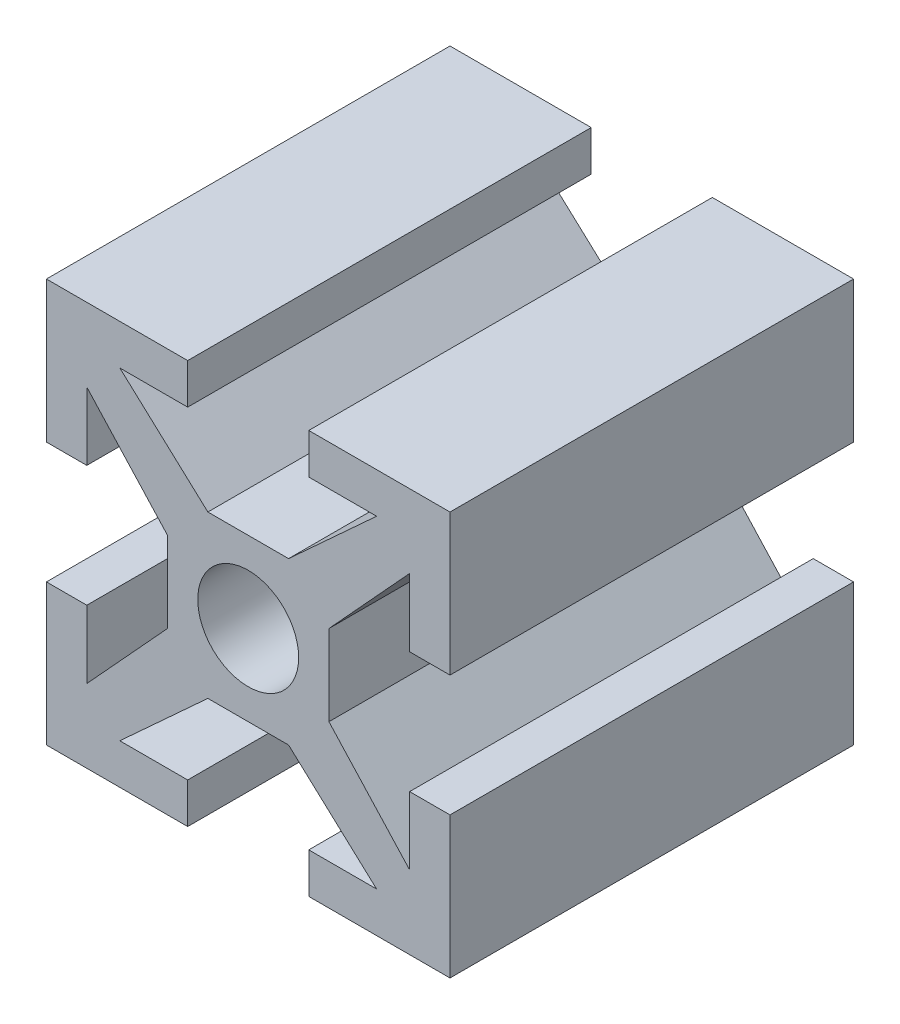
SolidWorks part; units mm, degrees
ref_plane "Front Plane" through (0, 0, 0) normal (0, 0, 1) x (1, 0, 0)
ref_plane "Top Plane" through (0, 0, 0) normal (0, 1, 0) x (1, 0, 0)
ref_plane "Right Plane" through (0, 0, 0) normal (1, 0, 0) x (0, 0, -1)
sketch "Sketch1" plane through (0, 0, 0) normal (0, 0, 1) x (1, 0, 0)
  line L0 (-4.0492, 2) -> (2, 2) construction
  line L1 (2, 2) -> (2, -4.2486) construction
  line L2 (0, 0) -> (0, 5) construction
  line L3 (0, 0) -> (6.7008, 0) construction
  line L4 (-4.0492, 5) -> (5, 5) construction
  line L5 (5, 5) -> (5, -5.8095) construction
  line L6 (1.5, 5) -> (5, 5)
  line L7 (5, 5) -> (5, 1.5)
  line L8 (5, 1.5) -> (4, 1.5)
  line L9 (4, 1.5) -> (4, 3.1816)
  line L10 (4, 3.1816) -> (2, 1)
  line L11 (2, 1) -> (2, 0)
  line L12 (1.5, 5) -> (1.5, 4)
  line L13 (1.5, 4) -> (3.1816, 4)
  line L14 (3.1816, 4) -> (1, 2)
  line L15 (1, 2) -> (0, 2)
  line L16 (0, 0) -> (7.554, 7.554) construction
  line L17 (5, -1.5) -> (5, -5)
  line L18 (5, -5) -> (1.5, -5)
  line L19 (1.5, -5) -> (1.5, -4)
  line L20 (1.5, -4) -> (3.1816, -4)
  line L21 (3.1816, -4) -> (1, -2)
  line L22 (1, -2) -> (0, -2)
  line L23 (5, -1.5) -> (4, -1.5)
  line L24 (4, -1.5) -> (4, -3.1816)
  line L25 (4, -3.1816) -> (2, -1)
  line L26 (2, -1) -> (2, 0)
  line L27 (0, 0) -> (5, 0) construction
  line L28 (-1.5, -5) -> (-5, -5)
  line L29 (-5, -5) -> (-5, -1.5)
  line L30 (-5, -1.5) -> (-4, -1.5)
  line L31 (-4, -1.5) -> (-4, -3.1816)
  line L32 (-4, -3.1816) -> (-2, -1)
  line L33 (-2, -1) -> (-2, 0)
  line L34 (-1.5, -5) -> (-1.5, -4)
  line L35 (-1.5, -4) -> (-3.1816, -4)
  line L36 (-3.1816, -4) -> (-1, -2)
  line L37 (-1, -2) -> (0, -2)
  line L38 (0, 0) -> (0, -5) construction
  line L39 (-5, 1.5) -> (-5, 5)
  line L40 (-5, 5) -> (-1.5, 5)
  line L41 (-1.5, 5) -> (-1.5, 4)
  line L42 (-1.5, 4) -> (-3.1816, 4)
  line L43 (-3.1816, 4) -> (-1, 2)
  line L44 (-1, 2) -> (0, 2)
  line L45 (-5, 1.5) -> (-4, 1.5)
  line L46 (-4, 1.5) -> (-4, 3.1816)
  line L47 (-4, 3.1816) -> (-2, 1)
  line L48 (-2, 1) -> (-2, 0)
  line L49 (0, 0) -> (-5, 0) construction
  circle A0 centre (0, 0) radius 1.25
  point P60 (0, 0)
  dimension "D10" = 4
  dimension "D11" = 2.5
  dimension "D1" = 2
  dimension "D2" = 2
  dimension "D3" = 5
  dimension "D4" = 5
  dimension "D5" = 1
  dimension "D6" = 1
  dimension "D7" = 3.5
  dimension "D8" = 3.5
  dimension "D9" = 1
extrude "Boss-Extrude2" add sketch "Sketch1" along normal blind 10 contours L47 L48 L33 L32 L31 L30 L29 L28 L34 L35 L36 L37 L22 L21 L20 L19 L18 L17 L23 L24 L25 L26 L11 L10 L9 L8 L7 L6 L12 L13 L14 L15 L44 L43 L42 L41 L40 L39 L45 L46 A0
